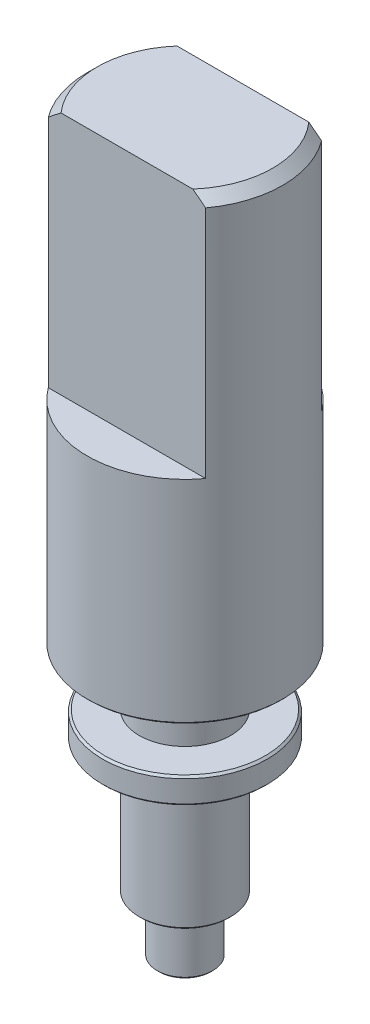
SolidWorks part; units mm, degrees
material "Латунь ЛС59  ГОСТ 15527-70"
ref_plane "Спереди" through (0, 0, 0) normal (0, 0, 1) x (1, 0, 0)
ref_plane "Сверху" through (0, 0, 0) normal (0, 1, 0) x (1, 0, 0)
ref_plane "Справа" through (0, 0, 0) normal (1, 0, 0) x (0, 0, -1)
sketch "Эскиз1" plane through (0, 0, 0) normal (0, 0, 1) x (1, 0, 0)
  line L0 (0, 18.3) -> (0, 0)
  line L1 (0, 0) -> (-0.7, 0)
  line L2 (-0.7, 0) -> (-0.7, 1.4)
  line L3 (-1.15, 4.75) -> (-2.075, 4.75)
  line L4 (-2.075, 4.75) -> (-2.075, 5.4)
  line L5 (-2.075, 5.4) -> (-1.15, 5.4)
  line L6 (-1.15, 5.4) -> (-1.15, 6.8)
  line L7 (-1.15, 6.8) -> (-2.46, 6.8)
  line L8 (-2.46, 6.8) -> (-2.46, 18.3)
  line L9 (-2.46, 18.3) -> (0, 18.3)
  line L10 (-0.7, 1.4) -> (-1.15, 1.4)
  line L11 (-1.15, 1.4) -> (-1.15, 4.75)
  dimension "D1" = 18.3
  dimension "D2" = 0.7
  dimension "D3" = 1.15
  dimension "D4" = 1.4
  dimension "D5" = 3.35
  dimension "D6" = 2.075
  dimension "D7" = 0.65
  dimension "D8" = 6.8
  dimension "D9" = 2.46
revolve "Повернуть1" add sketch "Эскиз1" angle 360 about L0
sketch "Эскиз2" plane through (0, 18.3, 0) normal (0, 1, 0) x (1, 0, 0)
  line L0 (-1.9799, 1.46) -> (1.9799, 1.46)
  line L1 (-1.9799, -1.46) -> (1.9799, -1.46)
  circle A0 centre (0, 0) radius 2.46 construction
  arc A1 (-1.9799, -1.46) -> (1.9799, -1.46) centre (0, 0) ccw
  arc A2 (1.9799, 1.46) -> (-1.9799, 1.46) centre (0, 0) ccw
  dimension "D1" = 1.46
  dimension "D2" = 2.92
extrude "Вырез-Вытянуть1" cut sketch "Эскиз2" against normal blind 6.15
chamfer "Фаска1" distance 0.25 angle 45 2 edges at (-2.46, 18.3, 0) (2.46, 18.3, 0)
chamfer "Фаска2" distance 0.05 angle 45 5 edges at (0, 0, 0.7) (0, 5.4, 2.075) (0, 4.75, 2.075) (0, 6.8, 2.46) (0, 1.4, 1.15)
sketch "Sketch1" plane through (0, 18.3, 0) normal (0, 1, 0) x (1, 0, 0)
  line L0 (0, 0) -> (36.012, 0) construction
  line L1 (0, 0) -> (0, -23.5838) construction
  circle A0 centre (0, 0) radius 2.475 construction
  circle A1 centre (0, 0) radius 2.475
sketch "Sketch2" plane through (0, 18.3, 0) normal (0, 1, 0) x (1, 0, 0)
  line L0 (-1.9799, 1.46) -> (1.9799, 1.46) construction
  line L1 (1.9799, -1.46) -> (-1.9799, -1.46) construction
  line L2 (-1.9799, 1.46) -> (1.9799, 1.46)
  line L3 (1.9799, -1.46) -> (-1.9799, -1.46)
  arc A0 (-1.9799, 1.46) -> (-1.9799, -1.46) centre (0, 0) ccw construction
  arc A1 (1.9799, -1.46) -> (1.9799, 1.46) centre (0, 0) ccw construction
  arc A2 (1.9799, 1.46) -> (-1.9799, 1.46) centre (0, 0) ccw construction
  arc A3 (-1.9799, -1.46) -> (1.9799, -1.46) centre (0, 0) ccw construction
  arc A4 (-1.9799, 1.46) -> (-1.9799, -1.46) centre (0, 0) ccw
  arc A5 (1.9799, -1.46) -> (1.9799, 1.46) centre (0, 0) ccw
  arc A6 (1.9799, 1.46) -> (-1.9799, 1.46) centre (0, 0) ccw
  arc A7 (-1.9799, -1.46) -> (1.9799, -1.46) centre (0, 0) ccw
